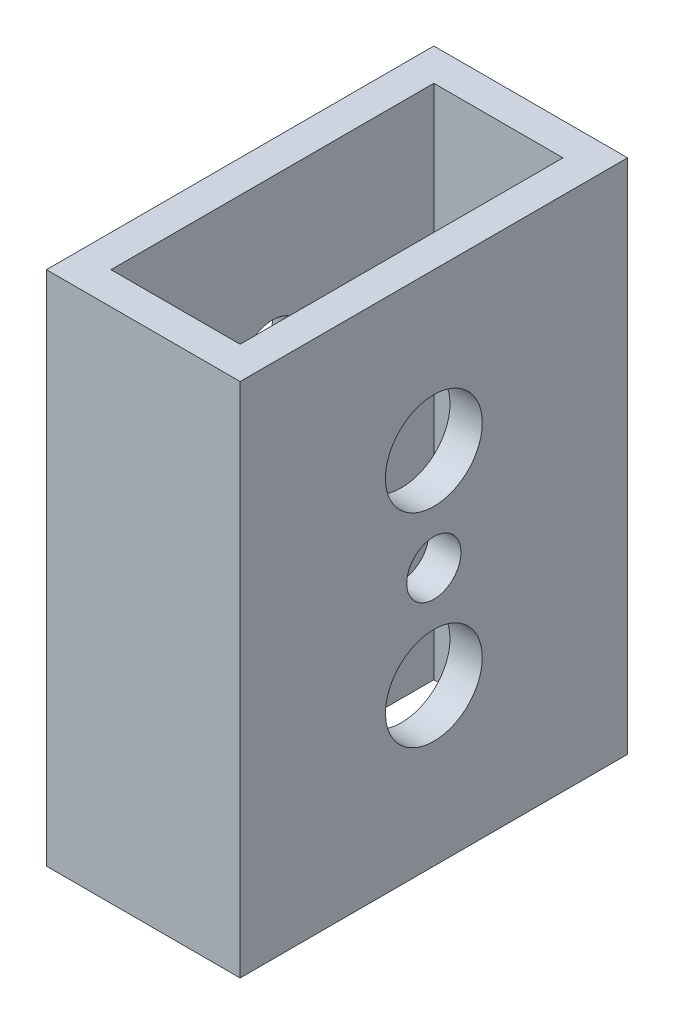
SolidWorks part; units mm, degrees
ref_plane "Front" through (0, 0, 0) normal (0, 0, 1) x (1, 0, 0)
ref_plane "Top" through (0, 0, 0) normal (0, 1, 0) x (1, 0, 0)
ref_plane "Right" through (0, 0, 0) normal (1, 0, 0) x (0, 0, -1)
sketch "Sketch1" plane through (0, 0, 0) normal (0, 1, 0) x (1, 0, 0)
  line L0 (3.175, 3.175) -> (15.875, 3.175)
  line L1 (0, 0) -> (19.05, 0)
  line L2 (0, 0) -> (0, 38.1)
  line L3 (0, 38.1) -> (19.05, 38.1)
  line L4 (19.05, 0) -> (19.05, 38.1)
  line L5 (15.875, 3.175) -> (15.875, 34.925)
  line L6 (3.175, 34.925) -> (15.875, 34.925)
  line L7 (3.175, 3.175) -> (3.175, 34.925)
  dimension "D1" = 38.1
  dimension "D2" = 19.05
  dimension "D3" = 3.175
extrude "Boss-Extrude1" add sketch "Sketch1" along normal blind 50.8
sketch "Sketch2" plane through (19.05, 0, 0) normal (1, 0, 0) x (0, 0, -1)
  line L0 (19.05, 0) -> (19.05, 15.4) construction
  line L1 (0, 0) -> (38.1, 0) construction
  line L2 (19.05, 15.4) -> (19.05, 35.4) construction
  line L3 (19.05, 35.4) -> (19.05, 50.8) construction
  line L6 (0, 50.8) -> (38.1, 50.8) construction
  circle A0 centre (19.05, 15.4) radius 3.175
  circle A1 centre (19.05, 35.4) radius 3.175
  dimension "D2" = 6.35
  dimension "D3" = 20
extrude "Cut-Extrude1" cut sketch "Sketch2" against normal through all
sketch "Sketch3" plane through (19.05, 0, 0) normal (1, 0, 0) x (0, 0, -1)
  circle A4 centre (19.05, 15.4) radius 4.7625
  circle A5 centre (19.05, 35.4) radius 4.7625
  dimension "D1" = 9.525
extrude "Cut-Extrude2" cut sketch "Sketch3" against normal up to next
ref_plane "Mid_Plane" through (0, 0, -19.05) normal (0, 0, -1) x (-1, 0, 0)
sketch "Sketch4" plane through (0, 0, 0) normal (-1, 0, 0) x (0, 0, 1)
  line L0 (-19.05, 18.575) -> (-19.05, 32.225) construction
  circle A0 centre (-19.05, 15.4) radius 3.175 construction
  circle A1 centre (-19.05, 35.4) radius 3.175 construction
  circle A2 centre (-19.05, 25.4) radius 2.667
  dimension "D1" = 5.334
extrude "Cut-Extrude3" cut sketch "Sketch4" against normal through all
sketch "Sketch5" plane through (0, 0, 0) normal (-1, 0, 0) x (0, 0, 1)
  circle A0 centre (-19.05, 25.4) radius 4.7625
  dimension "D1" = 9.525
extrude "Cut-Extrude4" cut sketch "Sketch5" against normal up to next
